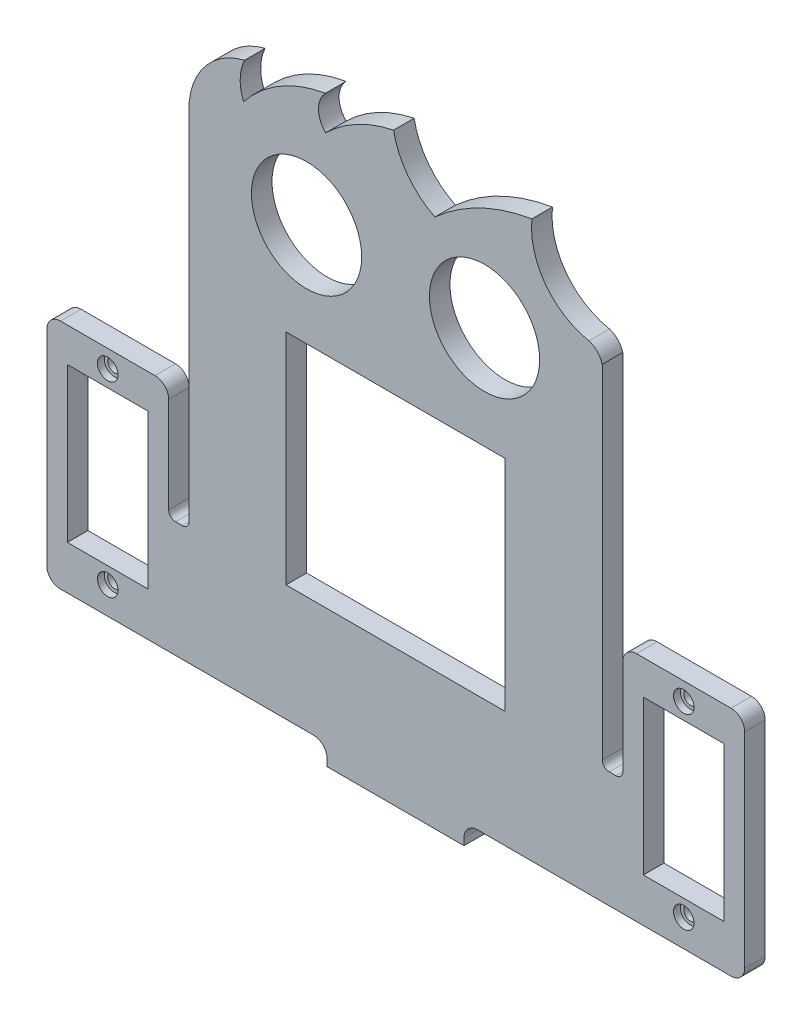
SolidWorks part; units mm, degrees
ref_plane "Alzado" through (0, 0, 0) normal (0, 0, 1) x (1, 0, 0)
ref_plane "Planta" through (0, 0, 0) normal (0, 1, 0) x (1, 0, 0)
ref_plane "Vista lateral" through (0, 0, 0) normal (1, 0, 0) x (0, 0, -1)
sketch "Model" plane through (0, 0, 0) normal (0, 0, 1) x (1, 0, 0)
  line L0 (68.699, -55.021) -> (68.699, -56.021)
  line L1 (48.699, -56.021) -> (68.699, -56.021)
  line L2 (26.5553, -36.0989) -> (27.5553, -36.0989)
  line L3 (90.899, -36.071) -> (89.8953, -36.071)
  line L4 (25.5553, -21.121) -> (25.5553, -35.0989)
  line L5 (91.899, -21.121) -> (91.899, -35.071)
  line L6 (88.8953, -35.071) -> (88.8953, 14.9836)
  line L7 (28.5553, -35.0989) -> (28.5553, 17.979)
  line L8 (58.699, -36.021) -> (58.699, -56.021) construction
  line L14 (74.699, -36.021) -> (74.699, -4.021)
  line L15 (74.699, -4.021) -> (42.699, -4.021)
  line L16 (42.699, -4.021) -> (42.699, -36.021)
  line L17 (42.699, -36.021) -> (74.699, -36.021)
  line L18 (94.899, -46.621) -> (106.699, -46.621)
  line L19 (106.699, -24.121) -> (94.899, -24.121)
  line L20 (94.899, -24.121) -> (94.899, -46.621)
  line L21 (10.7553, -24.121) -> (10.7553, -46.621)
  line L22 (10.7553, -46.621) -> (22.5553, -46.621)
  line L23 (22.5553, -46.621) -> (22.5553, -24.121)
  line L24 (22.5553, -24.121) -> (10.7553, -24.121)
  line L54 (46.699, -53.021) -> (9.699, -53.0206)
  line L57 (107.699, -53.021) -> (70.699, -53.021)
  line L61 (107.699, -19.121) -> (93.899, -19.121)
  line L62 (109.699, -51.021) -> (109.699, -21.121)
  line L92 (7.7553, -21.121) -> (7.7553, -51.0769)
  line L93 (23.5553, -19.121) -> (9.7553, -19.121)
  line L99 (48.699, -55.021) -> (48.699, -56.021)
  line L102 (106.699, -46.621) -> (106.699, -24.121)
  arc A0 (27.5553, -36.0989) -> (28.5553, -35.0989) centre (27.5553, -35.0989) ccw
  arc A1 (26.5553, -36.0989) -> (25.5553, -35.0989) centre (26.5553, -35.0989) cw
  arc A2 (89.8953, -36.071) -> (88.8953, -35.071) centre (89.8953, -35.071) cw
  arc A3 (90.899, -36.071) -> (91.899, -35.071) centre (90.899, -35.071) ccw
  arc A6 (68.699, -55.021) -> (70.699, -53.021) centre (70.699, -55.021) cw
  arc A7 (48.699, -55.021) -> (46.699, -53.021) centre (46.699, -55.021) ccw
  circle A8 centre (71.699, 10.979) radius 8.05
  circle A9 centre (45.699, 10.979) radius 8.05
  circle A10 centre (100.799, -21.721) radius 1
  circle A11 centre (100.799, -49.021) radius 1
  circle A12 centre (16.6553, -49.021) radius 1
  circle A13 centre (16.6553, -21.721) radius 1
  arc A36 (36.6464, 27.3235) -> (28.5553, 17.979) centre (39.1528, 16.978) ccw
  arc A37 (36.6464, 27.3235) -> (36.4994, 22.0007) centre (42.5214, 24.4978) ccw
  arc A38 (48.467, 29.056) -> (36.4994, 22.0007) centre (51.655, 9.9705) ccw
  arc A39 (48.467, 29.056) -> (48.49, 24.056) centre (50.9785, 26.5675) ccw
  arc A40 (58.4156, 29.366) -> (48.49, 24.056) centre (62.4081, 9.9713) ccw
  arc A41 (58.4156, 29.366) -> (64.4524, 21.3937) centre (69.4063, 31.4167) ccw
  arc A42 (78.6205, 28.2411) -> (64.4524, 21.3937) centre (83.1982, 0.6878) ccw
  arc A43 (78.6205, 28.2411) -> (86.965, 16.978) centre (88.866, 27.109) ccw
  arc A44 (88.8953, 14.9836) -> (86.965, 16.978) centre (86.0189, 14.1311) ccw
  arc A47 (93.899, -19.121) -> (91.899, -21.121) centre (93.899, -21.121) ccw
  arc A48 (109.699, -21.121) -> (107.699, -19.121) centre (107.699, -21.121) ccw
  arc A49 (107.699, -53.021) -> (109.699, -51.021) centre (107.699, -51.021) ccw
  arc A66 (7.7553, -51.0769) -> (9.699, -53.0206) centre (9.699, -51.0769) ccw
  arc A67 (9.7553, -19.121) -> (7.7553, -21.121) centre (9.7553, -21.121) ccw
  arc A68 (25.5553, -21.121) -> (23.5553, -19.121) centre (23.5553, -21.121) ccw
  dimension "D1" = 1
  dimension "D2" = 2
extrude "Saliente-Extruir1" add sketch "Model" along normal blind 3
sketch "Croquis2" plane through (0, 0, 3) normal (0, 0, 1) x (1, 0, 0)
  line L0 (48.699, -56.021) -> (48.699, -53.021)
  line L1 (48.699, -53.021) -> (68.699, -53.021)
  line L2 (68.699, -53.021) -> (68.699, -56.021)
  line L3 (68.699, -56.021) -> (48.699, -56.021)
  dimension "D1" = 3
extrude "Saliente-Extruir2" add sketch "Croquis2" against normal blind 11
sketch "Croquis3" plane through (0, -53.021, 0) normal (0, 1, 0) x (1, 0, 0)
  line L0 (58.699, 8) -> (58.699, -3) construction
  line L1 (68.699, 8) -> (48.699, 8) construction
  line L2 (68.699, -3) -> (48.699, -3) construction
  circle A0 centre (52.699, 3.5) radius 1.5
  circle A1 centre (64.699, 3.5) radius 1.5
  dimension "D1" = 6
  dimension "D2" = 6.5
extrude "Cortar-Extruir1" cut sketch "Croquis3" against normal blind 3
fillet "Redondeo1" radius 2 2 edges at (68.699, -54.521, -8) (48.699, -54.521, -8)
sketch "Croquis4" plane through (0, -53.021, 0) normal (0, 1, 0) x (1, 0, 0)
  circle A0 centre (52.699, 3.5) radius 2.25
  circle A1 centre (64.699, 3.5) radius 2.25
extrude "Cortar-Extruir2" cut sketch "Croquis4" against normal blind 1
sketch "Croquis6" plane through (0, 0, 3) normal (0, 0, 1) x (1, 0, 0)
  circle A0 centre (16.6553, -21.721) radius 1.5
  circle A1 centre (16.6553, -49.021) radius 1.5
  circle A2 centre (100.799, -49.021) radius 1.5
  circle A3 centre (100.799, -21.721) radius 1.5
extrude "Cortar-Extruir4" cut sketch "Croquis6" against normal blind 1
